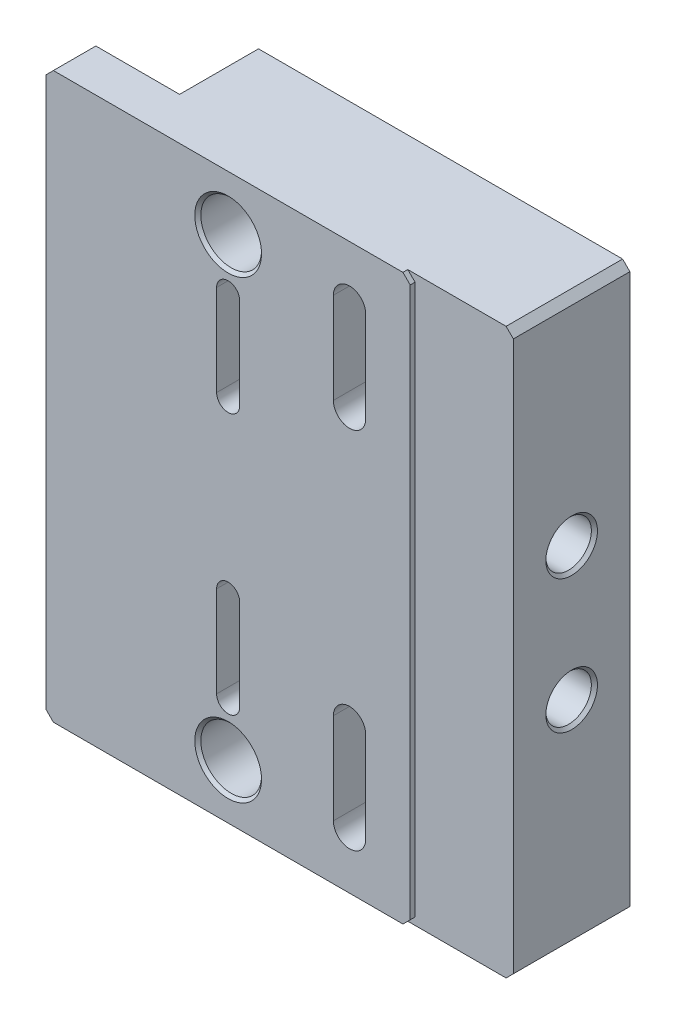
SolidWorks part; units mm, degrees
material "6061-T6 Al"
ref_plane "Front Plane" through (0, 0, 0) normal (0, 0, 1) x (1, 0, 0)
ref_plane "Top Plane" through (0, 0, 0) normal (0, 1, 0) x (1, 0, 0)
ref_plane "Right Plane" through (0, 0, 0) normal (1, 0, 0) x (0, 0, -1)
sketch "Sketch6" plane through (0, 0, 0) normal (0, 0, 1) x (1, 0, 0)
  line L1 (0, 0) -> (58.674, 0) construction
  line L2 (-36.576, 59.055) -> (57.15, 59.055)
  line L3 (-38.1, 57.531) -> (-38.1, -57.531)
  line L4 (-36.576, -59.055) -> (57.15, -59.055)
  line L5 (58.674, 57.531) -> (58.674, -57.531)
  line L6 (-2.413, 36.83) -> (0, 27.305) construction
  line L7 (0, 27.305) -> (2.413, 17.78) construction
  line L8 (-2.413, 36.83) -> (-2.413, 17.78) construction
  line L9 (2.413, 36.83) -> (2.413, 17.78) construction
  line L10 (-2.413, -36.83) -> (-2.413, -17.78) construction
  line L11 (2.413, -36.83) -> (2.413, -17.78) construction
  line L12 (0, 27.305) -> (0, -27.305) construction
  line L13 (-38.1, 57.531) -> (-36.576, 59.055)
  line L14 (57.15, 59.055) -> (58.674, 57.531)
  line L15 (57.15, -59.055) -> (58.674, -57.531)
  line L16 (-38.1, -57.531) -> (-36.576, -59.055)
  arc A2 (-2.413, 36.83) -> (2.413, 36.83) centre (0, 36.83) cw construction
  arc A4 (-2.413, 17.78) -> (2.413, 17.78) centre (0, 17.78) ccw construction
  arc A5 (-2.413, -17.78) -> (2.413, -17.78) centre (0, -17.78) cw construction
  arc A6 (-2.413, -36.83) -> (2.413, -36.83) centre (0, -36.83) ccw construction
  dimension "D1" = 118.11
  dimension "D2" = 38.1
  dimension "D3" = 19.05
  dimension "D4" = 4.826
  dimension "D5" = 58.674
  dimension "D6" = 54.61
  dimension "D7" = 1.524
extrude "Boss-Extrude1" add sketch "Sketch6" against normal blind 25.4
hole_wizard "1/2-13 Tapped Hole1" positions "Sketch8" profile "Sketch7" tap size "1/2-13" standard "ANSI Inch" end condition through all
sketch "Sketch8" plane through (-4.2249, 38.992, -25.4) normal (0, 0, 1) x (1, 0, 0)
  line L0 (4.2249, -38.992) -> (62.8989, -38.992) construction
  line L1 (4.2249, -38.992) -> (62.8989, -38.992) construction
  point P0 (4.2249, 8.633)
  point P2 (4.2249, -86.617)
  dimension "D1" = 95.25
sketch "Sketch7" plane through (0, 47.625, -25.4) normal (1, 0, 0) x (0, 1, 0)
  line L0 (0, 0) -> (0, 25.4)
  line L1 (0, 25.4) -> (6.985, 25.4)
  line L2 (6.35, 24.765) -> (6.35, 0.635)
  line L3 (6.35, 0.635) -> (6.985, 0)
  line L5 (6.985, 0) -> (0, 0)
  line L6 (-6.35, 0.635) -> (-6.985, 0) construction
  line L7 (6.985, 25.4) -> (6.35, 24.765)
  line L8 (-6.985, 25.4) -> (-6.35, 24.765) construction
  line L11 (0, -6.35) -> (0, 107.95) construction
  dimension "Thread Major Dia." = 12.7
  dimension "Thru Tap Drill Depth" = 25.4
  dimension "Near C'Sink Dia." = 13.97
  dimension "Near C'Sink Angle" = 90
  dimension "Far C'Sink Dia." = 13.97
  dimension "Far C'Sink Angle" = 90
sketch "Sketch9" plane through (0, 0, 0) normal (0, 0, -1) x (-1, 0, 0)
  line L4 (0, 17.78) -> (0, 36.83) construction
  line L5 (-2.413, 17.78) -> (-2.413, 36.83)
  line L6 (2.413, 17.78) -> (2.413, 36.83)
  line L7 (0, -17.78) -> (0, -36.83) construction
  line L8 (2.413, -17.78) -> (2.413, -36.83)
  line L9 (-2.413, -17.78) -> (-2.413, -36.83)
  arc A4 (-2.413, 17.78) -> (2.413, 17.78) centre (0, 17.78) ccw
  arc A5 (2.413, 36.83) -> (-2.413, 36.83) centre (0, 36.83) ccw
  arc A6 (2.413, -17.78) -> (-2.413, -17.78) centre (0, -17.78) ccw
  arc A7 (-2.413, -36.83) -> (2.413, -36.83) centre (0, -36.83) ccw
  arc A8 (-2.413, 17.78) -> (2.413, 17.78) centre (0, 17.78) ccw construction
  point P2 (0, 27.305)
  point P7 (0, -27.305)
extrude "Cut-Extrude1" cut sketch "Sketch9" along normal blind 5.842
sketch "Sketch12" plane through (0, 0, 0) normal (0, 0, 1) x (1, 0, 0)
  line L0 (38.1, 57.531) -> (38.1, -57.531)
  line L1 (0, 27.305) -> (0, -27.305) construction
  line L2 (0, 27.305) -> (0, -27.305) construction
  line L3 (-38.1, 57.531) -> (-38.1, -57.531) construction
  line L4 (36.576, 59.055) -> (38.1, 57.531)
  line L5 (57.15, 59.055) -> (-36.576, 59.055) construction
  line L6 (38.1, -57.531) -> (36.576, -59.055)
  line L7 (-36.576, -59.055) -> (57.15, -59.055) construction
  line L8 (-36.576, 59.055) -> (-38.1, 57.531)
  line L9 (-38.1, 57.531) -> (-38.1, -57.531)
  line L10 (-38.1, -57.531) -> (-36.576, -59.055)
  line L11 (-36.576, -59.055) -> (57.15, -59.055)
  line L12 (57.15, -59.055) -> (58.674, -57.531)
  line L13 (58.674, -57.531) -> (58.674, 57.531)
  line L14 (58.674, 57.531) -> (57.15, 59.055)
  line L15 (57.15, 59.055) -> (-36.576, 59.055)
  line L19 (36.576, -59.055) -> (57.15, -59.055)
  line L20 (57.15, -59.055) -> (58.674, -57.531)
  line L21 (58.674, -57.531) -> (58.674, 57.531)
  line L22 (58.674, 57.531) -> (57.15, 59.055)
  line L23 (57.15, 59.055) -> (36.576, 59.055)
  dimension "D1" = 0
extrude "Cut-Extrude2" cut sketch "Sketch12" against normal blind 1.016
hole_wizard "3/8-16 Tapped Hole1" positions "Sketch11" profile "Sketch10" tap size "3/8-16" standard "ANSI Inch"
sketch "Sketch11" plane through (58.674, 0, 0) normal (1, 0, 0) x (0, 0, -1)
  line L0 (13.208, 57.531) -> (13.208, 13.97) construction
  line L1 (25.4, 57.531) -> (1.016, 57.531) construction
  line L2 (13.208, 13.97) -> (13.208, 0) construction
  line L3 (13.208, 0) -> (13.208, -13.97) construction
  point P1 (13.208, 13.97)
  point P9 (13.208, -13.97)
  dimension "D1" = 27.94
sketch "Sketch10" plane through (58.674, 13.97, -13.208) normal (0, 1, 0) x (0, 0, -1)
  line L0 (0, 0) -> (0, 27.9879)
  line L1 (0, 27.9879) -> (3.9687, 25.6032)
  line L2 (3.9687, 25.6032) -> (3.9687, 21.59)
  line L3 (3.9687, 21.59) -> (4.7625, 21.59)
  line L5 (4.7625, 21.59) -> (4.7625, 0.635)
  line L6 (4.7625, 0.635) -> (5.3975, 0)
  line L7 (5.3975, 0) -> (0, 0)
  line L8 (-4.7625, 0.635) -> (-5.3975, 0) construction
  line L10 (0, 27.9879) -> (-3.9688, 25.6032) construction
  line L11 (0, -6.35) -> (0, 107.95) construction
  dimension "Tap Drill Dia." = 7.9375
  dimension "Tap Drill Depth" = 25.6032
  dimension "Thread Major Dia." = 9.525
  dimension "Thread Depth" = 21.59
  dimension "Near C'Sink Dia." = 10.795
  dimension "Near C'Sink Angle" = 90
  dimension "Drill Angle" = 118
sketch "Sketch13" plane through (0, 0, 0) normal (0, 0, 1) x (1, 0, 0)
  line L0 (25.4, 47.625) -> (25.4, 28.575) construction
  line L1 (28.7782, 47.625) -> (28.7782, 28.575)
  line L2 (22.0218, 47.625) -> (22.0218, 28.575)
  line L3 (2.413, 36.83) -> (2.413, 17.78) construction
  line L5 (25.4, -28.575) -> (25.4, -47.625) construction
  line L6 (0, 0) -> (25.4, 0) construction
  line L7 (0, 27.305) -> (0, -27.305) construction
  line L9 (28.7782, -28.575) -> (28.7782, -47.625)
  line L10 (22.0218, -28.575) -> (22.0218, -47.625)
  arc A0 (28.7782, 47.625) -> (22.0218, 47.625) centre (25.4, 47.625) ccw
  arc A1 (22.0218, 28.575) -> (28.7782, 28.575) centre (25.4, 28.575) ccw
  arc A2 (28.7782, -28.575) -> (22.0218, -28.575) centre (25.4, -28.575) ccw
  arc A3 (22.0218, -47.625) -> (28.7782, -47.625) centre (25.4, -47.625) ccw
  point P2 (25.4, 38.1)
  point P11 (25.4, -38.1)
  dimension "D3" = 6.7564
  dimension "D1" = 76.2
  dimension "D2" = 25.4
extrude "Cut-Extrude3" cut sketch "Sketch13" against normal through all
sketch "Sketch14" plane through (0, 0, -25.4) normal (0, 0, 1) x (1, 0, 0)
  line L0 (25.4, 47.625) -> (25.4, 28.575) construction
  line L1 (32.5438, 47.625) -> (32.5438, 28.575)
  line L2 (18.2562, 47.625) -> (18.2562, 28.575)
  line L3 (25.4, -28.575) -> (25.4, -47.625) construction
  line L4 (32.5437, -28.575) -> (32.5438, -47.625)
  line L5 (18.2563, -28.575) -> (18.2563, -47.625)
  arc A0 (32.5438, 47.625) -> (18.2562, 47.625) centre (25.4, 47.625) ccw
  arc A1 (18.2562, 28.575) -> (32.5438, 28.575) centre (25.4, 28.575) ccw
  arc A2 (32.5437, -28.575) -> (18.2563, -28.575) centre (25.4, -28.575) ccw
  arc A3 (18.2563, -47.625) -> (32.5438, -47.625) centre (25.4, -47.625) ccw
  point P4 (25.4, 38.1)
  point P11 (25.4, -38.1)
  dimension "D1" = 14.2875
extrude "Cut-Extrude4" cut sketch "Sketch14" along normal blind 10.668
sketch "Sketch15" plane through (0, -59.055, 0) normal (0, -1, 0) x (1, 0, 0)
  line L0 (-38.1, -25.4) -> (-38.1, 0) construction
  line L1 (-19.05, -8.89) -> (-38.1, -8.89)
  line L2 (-19.05, -8.89) -> (-19.05, -25.4)
  line L3 (-19.05, -25.4) -> (-38.1, -25.4)
  line L4 (-38.1, -8.89) -> (-38.1, -25.4)
  line L5 (-36.576, -25.4) -> (57.15, -25.4) construction
  dimension "D1" = 16.51
  dimension "D2" = 19.05
extrude "Cut-Extrude5" cut sketch "Sketch15" against normal through all
